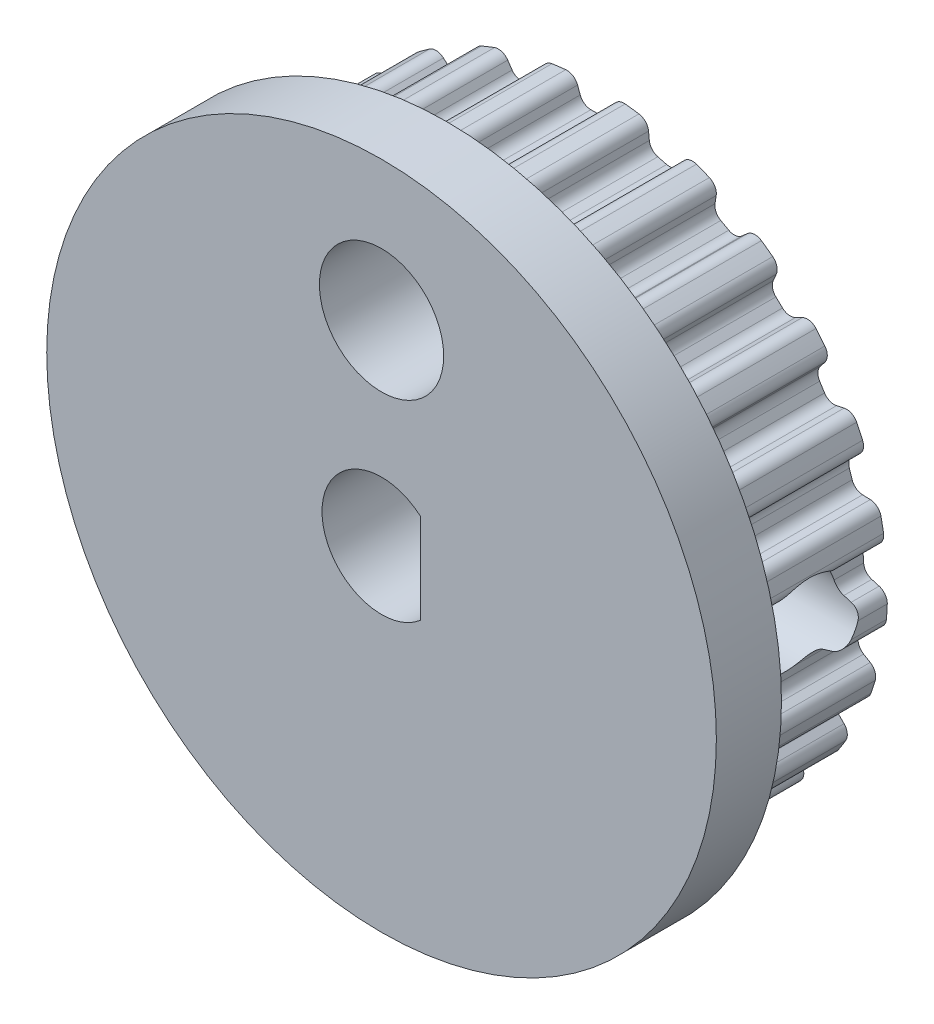
SolidWorks part; units mm, degrees
ref_plane "Front Plane" through (0, 0, 0) normal (0, 0, 1) x (1, 0, 0)
ref_plane "Top Plane" through (0, 0, 0) normal (0, 1, 0) x (1, 0, 0)
ref_plane "Right Plane" through (0, 0, 0) normal (1, 0, 0) x (0, 0, -1)
ref_plane "Plane1" through (0, 0, -5.3) normal (0, 0, -1) x (-1, 0, 0)
sketch "Sketch1" plane through (0, 0, -5.3) normal (0, 0, -1) x (-1, 0, 0)
  line L0 (-2.7705, -6.663) -> (-2.5415, -6.7537)
  line L1 (-2.3491, -7.0456) -> (-2.3549, -7.2528)
  line L2 (-1.4305, -7.4901) -> (-1.3357, -7.3057)
  line L3 (-1.0264, -7.1427) -> (-0.7821, -7.1735)
  line L4 (-0.5231, -7.4084) -> (-0.4772, -7.6106)
  line L5 (0.4772, -7.6106) -> (0.5231, -7.4084)
  line L6 (0.7821, -7.1735) -> (1.0264, -7.1427)
  line L7 (1.3357, -7.3057) -> (1.4305, -7.4901)
  line L8 (2.3549, -7.2528) -> (2.3491, -7.0456)
  line L9 (2.5415, -6.7537) -> (2.7705, -6.663)
  line L10 (3.1106, -6.744) -> (3.2483, -6.8991)
  line L11 (4.0846, -6.4393) -> (4.0274, -6.24)
  line L12 (4.1413, -5.9094) -> (4.3405, -5.7647)
  line L13 (4.6901, -5.7586) -> (4.862, -5.8745)
  line L14 (5.5576, -5.2212) -> (5.4527, -5.0424)
  line L15 (5.4808, -4.6939) -> (5.6377, -4.5041)
  line L16 (5.9748, -4.4113) -> (6.1701, -4.4808)
  line L17 (6.6815, -3.6751) -> (6.5354, -3.528)
  line L18 (6.4759, -3.1834) -> (6.5808, -2.9606)
  line L19 (6.8842, -2.7868) -> (7.0906, -2.8056)
  line L20 (7.3855, -1.898) -> (7.2075, -1.7918)
  line L21 (7.0641, -1.4729) -> (7.1103, -1.231)
  line L22 (7.3609, -0.9872) -> (7.5656, -0.9541)
  line L23 (7.6255, -0.0016) -> (7.4266, 0.0569)
  line L24 (7.2085, 0.3301) -> (7.193, 0.5759)
  line L25 (7.3752, 0.8744) -> (7.5652, 0.9574)
  line L26 (7.3864, 1.8948) -> (7.1792, 1.902)
  line L27 (6.8999, 2.1125) -> (6.8238, 2.3467)
  line L28 (6.9261, 2.681) -> (7.0894, 2.8087)
  line L29 (6.6831, 3.6722) -> (6.4806, 3.6277)
  line L30 (6.1578, 3.762) -> (6.0259, 3.9699)
  line L31 (6.0417, 4.3192) -> (6.1682, 4.4835)
  line L32 (5.5599, 5.2188) -> (5.3748, 5.1254)
  line L33 (5.0288, 5.1752) -> (4.8493, 5.3438)
  line L34 (4.7777, 5.6861) -> (4.8594, 5.8766)
  line L35 (4.0874, 6.4376) -> (3.9314, 6.301)
  line L36 (3.5837, 6.2632) -> (3.368, 6.3819)
  line L37 (3.2136, 6.6956) -> (3.2453, 6.9005)
  line L38 (2.358, 7.2518) -> (2.2409, 7.0807)
  line L39 (1.9136, 6.9577) -> (1.675, 7.0189)
  line L40 (1.4475, 7.2844) -> (1.4273, 7.4908)
  line L41 (0.4805, 7.6104) -> (0.4095, 7.4156)
  line L42 (0.1231, 7.215) -> (-0.1231, 7.215)
  line L43 (-0.4095, 7.4156) -> (-0.4805, 7.6104)
  line L44 (-1.4273, 7.4908) -> (-1.4475, 7.2844)
  line L45 (-1.675, 7.0189) -> (-1.9136, 6.9577)
  line L46 (-2.2409, 7.0807) -> (-2.358, 7.2518)
  line L47 (-3.2453, 6.9005) -> (-3.2136, 6.6956)
  line L48 (-3.368, 6.3819) -> (-3.5837, 6.2632)
  line L49 (-3.9314, 6.301) -> (-4.0874, 6.4376)
  line L50 (-4.8594, 5.8766) -> (-4.7777, 5.6861)
  line L51 (-4.8493, 5.3438) -> (-5.0288, 5.1752)
  line L52 (-5.3748, 5.1254) -> (-5.5599, 5.2188)
  line L53 (-6.1682, 4.4835) -> (-6.0417, 4.3192)
  line L54 (-6.0259, 3.9699) -> (-6.1578, 3.762)
  line L55 (-6.4806, 3.6277) -> (-6.6831, 3.6722)
  line L56 (-7.0894, 2.8087) -> (-6.9261, 2.681)
  line L57 (-6.8238, 2.3467) -> (-6.8999, 2.1125)
  line L58 (-7.1792, 1.902) -> (-7.3864, 1.8948)
  line L59 (-7.5652, 0.9574) -> (-7.3752, 0.8744)
  line L60 (-7.193, 0.5759) -> (-7.2085, 0.3301)
  line L61 (-7.4266, 0.0569) -> (-7.6255, -0.0016)
  line L62 (-7.5656, -0.9541) -> (-7.3609, -0.9872)
  line L63 (-7.1103, -1.231) -> (-7.0641, -1.4729)
  line L64 (-7.2075, -1.7918) -> (-7.3855, -1.898)
  line L65 (-7.0906, -2.8056) -> (-6.8842, -2.7868)
  line L66 (-6.5808, -2.9606) -> (-6.4759, -3.1834)
  line L67 (-6.5354, -3.528) -> (-6.6815, -3.6751)
  line L68 (-6.1701, -4.4808) -> (-5.9748, -4.4113)
  line L69 (-5.6377, -4.5041) -> (-5.4808, -4.6939)
  line L70 (-5.4527, -5.0424) -> (-5.5576, -5.2212)
  line L71 (-4.862, -5.8745) -> (-4.6901, -5.7586)
  line L72 (-4.3405, -5.7647) -> (-4.1413, -5.9094)
  line L73 (-4.0274, -6.24) -> (-4.0846, -6.4393)
  line L74 (-3.2483, -6.8991) -> (-3.1106, -6.744)
  arc A2 (-2.5415, -6.7537) -> (-2.3491, -7.0456) centre (-2.6537, -7.0371) cw
  arc A3 (-2.3549, -7.2528) -> (-2.133, -7.5547) centre (-2.0502, -7.2613) ccw
  arc A4 (-2.133, -7.5547) -> (-1.7703, -7.6478) centre (0, 0) ccw
  arc A5 (-1.7703, -7.6478) -> (-1.4305, -7.4901) centre (-1.7016, -7.3508) ccw
  arc A6 (-1.3357, -7.3057) -> (-1.0264, -7.1427) centre (-1.0646, -7.4451) cw
  arc A7 (-0.7821, -7.1735) -> (-0.5231, -7.4084) centre (-0.8203, -7.4759) cw
  arc A8 (-0.4772, -7.6106) -> (-0.1872, -7.8478) centre (-0.1799, -7.5431) ccw
  arc A9 (-0.1872, -7.8478) -> (0.1872, -7.8478) centre (0, 0) ccw
  arc A10 (0.1872, -7.8478) -> (0.4772, -7.6106) centre (0.1799, -7.5431) ccw
  arc A11 (0.5231, -7.4084) -> (0.7821, -7.1735) centre (0.8203, -7.4759) cw
  arc A12 (1.0264, -7.1427) -> (1.3357, -7.3057) centre (1.0646, -7.4451) cw
  arc A13 (1.4305, -7.4901) -> (1.7703, -7.6478) centre (1.7016, -7.3508) ccw
  arc A14 (1.7703, -7.6478) -> (2.133, -7.5547) centre (0, 0) ccw
  arc A15 (2.133, -7.5547) -> (2.3549, -7.2528) centre (2.0502, -7.2613) ccw
  arc A16 (2.3491, -7.0456) -> (2.5415, -6.7537) centre (2.6537, -7.0371) cw
  arc A17 (2.7705, -6.663) -> (3.1106, -6.744) centre (2.8827, -6.9464) cw
  arc A18 (3.2483, -6.8991) -> (3.6166, -6.9672) centre (3.4762, -6.6967) ccw
  arc A19 (3.6166, -6.9672) -> (3.9447, -6.7869) centre (0, 0) ccw
  arc A20 (3.9447, -6.7869) -> (4.0846, -6.4393) centre (3.7916, -6.5233) ccw
  arc A21 (4.0274, -6.24) -> (4.1413, -5.9094) centre (4.3204, -6.156) cw
  arc A22 (4.3405, -5.7647) -> (4.6901, -5.7586) centre (4.5196, -6.0113) cw
  arc A23 (4.862, -5.8745) -> (5.2357, -5.8489) centre (5.0324, -5.6218) ccw
  arc A24 (5.2357, -5.8489) -> (5.5086, -5.5926) centre (0, 0) ccw
  arc A25 (5.5086, -5.5926) -> (5.5576, -5.2212) centre (5.2947, -5.3755) ccw
  arc A26 (5.4527, -5.0424) -> (5.4808, -4.6939) centre (5.7156, -4.8882) cw
  arc A27 (5.6377, -4.5041) -> (5.9748, -4.4113) centre (5.8726, -4.6984) cw
  arc A28 (6.1701, -4.4808) -> (6.5258, -4.3631) centre (6.2724, -4.1937) ccw
  arc A29 (6.5258, -4.3631) -> (6.7264, -4.047) centre (0, 0) ccw
  arc A30 (6.7264, -4.047) -> (6.6815, -3.6751) centre (6.4652, -3.8898) ccw
  arc A31 (6.5354, -3.528) -> (6.4759, -3.1834) centre (6.7517, -3.3132) cw
  arc A32 (6.5808, -2.9606) -> (6.8842, -2.7868) centre (6.8565, -3.0904) cw
  arc A33 (7.0906, -2.8056) -> (7.4058, -2.6031) centre (7.1183, -2.5021) ccw
  arc A34 (7.4058, -2.6031) -> (7.5215, -2.247) centre (0, 0) ccw
  arc A35 (7.5215, -2.247) -> (7.3855, -1.898) centre (7.2295, -2.1598) ccw
  arc A36 (7.2075, -1.7918) -> (7.0641, -1.4729) centre (7.3635, -1.53) cw
  arc A37 (7.1103, -1.231) -> (7.3609, -0.9872) centre (7.4097, -1.2881) cw
  arc A38 (7.5656, -0.9541) -> (7.8205, -0.6796) centre (7.5169, -0.6532) ccw
  arc A39 (7.8205, -0.6796) -> (7.844, -0.3059) centre (0, 0) ccw
  arc A40 (7.844, -0.3059) -> (7.6255, -0.0016) centre (7.5395, -0.294) ccw
  arc A41 (7.4266, 0.0569) -> (7.2085, 0.3301) centre (7.5127, 0.3493) cw
  arc A42 (7.193, 0.5759) -> (7.3752, 0.8744) centre (7.4972, 0.5951) cw
  arc A43 (7.5652, 0.9574) -> (7.7438, 1.2866) centre (7.4432, 1.2367) ccw
  arc A44 (7.7438, 1.2866) -> (7.6737, 1.6544) centre (0, 0) ccw
  arc A45 (7.6737, 1.6544) -> (7.3864, 1.8948) centre (7.3757, 1.5902) ccw
  arc A46 (7.1792, 1.902) -> (6.8999, 2.1125) centre (7.1898, 2.2066) cw
  arc A47 (6.8238, 2.3467) -> (6.9261, 2.681) centre (7.1137, 2.4408) cw
  arc A48 (7.0894, 2.8087) -> (7.1806, 3.172) centre (6.9018, 3.0489) ccw
  arc A49 (7.1806, 3.172) -> (7.0212, 3.5108) centre (0, 0) ccw
  arc A50 (7.0212, 3.5108) -> (6.6831, 3.6722) centre (6.7485, 3.3745) ccw
  arc A51 (6.4806, 3.6277) -> (6.1578, 3.762) centre (6.4152, 3.9254) cw
  arc A52 (6.0259, 3.9699) -> (6.0417, 4.3192) centre (6.2832, 4.1333) cw
  arc A53 (6.1682, 4.4835) -> (6.1661, 4.8581) centre (5.9267, 4.6695) ccw
  arc A54 (6.1661, 4.8581) -> (5.9275, 5.1466) centre (0, 0) ccw
  arc A55 (5.9275, 5.1466) -> (5.5599, 5.2188) centre (5.6973, 4.9468) ccw
  arc A56 (5.3748, 5.1254) -> (5.0288, 5.1752) centre (5.2374, 5.3974) cw
  arc A57 (4.8493, 5.3438) -> (4.7777, 5.6861) centre (5.0579, 5.566) cw
  arc A58 (4.8594, 5.8766) -> (4.7643, 6.2389) centre (4.5793, 5.9967) ccw
  arc A59 (4.7643, 6.2389) -> (4.4613, 6.459) centre (0, 0) ccw
  arc A60 (4.4613, 6.459) -> (4.0874, 6.4376) centre (4.2881, 6.2082) ccw
  arc A61 (3.9314, 6.301) -> (3.5837, 6.2632) centre (3.7306, 6.5303) cw
  arc A62 (3.368, 6.3819) -> (3.2136, 6.6956) centre (3.5148, 6.649) cw
  arc A63 (3.2453, 6.9005) -> (3.063, 7.2278) centre (2.9441, 6.9471) ccw
  arc A64 (3.063, 7.2278) -> (2.7149, 7.3656) centre (0, 0) ccw
  arc A65 (2.7149, 7.3656) -> (2.358, 7.2518) centre (2.6095, 7.0796) ccw
  arc A66 (2.2409, 7.0807) -> (1.9136, 6.9577) centre (1.9894, 7.2529) cw
  arc A67 (1.675, 7.0189) -> (1.4475, 7.2844) centre (1.7508, 7.3142) cw
  arc A68 (1.4273, 7.4908) -> (1.1693, 7.7624) centre (1.1239, 7.461) ccw
  arc A69 (1.1693, 7.7624) -> (0.7979, 7.8093) centre (0, 0) ccw
  arc A70 (0.7979, 7.8093) -> (0.4805, 7.6104) centre (0.7669, 7.5061) ccw
  arc A71 (0.4095, 7.4156) -> (0.1231, 7.215) centre (0.1231, 7.5198) cw
  arc A72 (-0.1231, 7.215) -> (-0.4095, 7.4156) centre (-0.1231, 7.5198) cw
  arc A73 (-0.4805, 7.6104) -> (-0.7979, 7.8093) centre (-0.7669, 7.5061) ccw
  arc A74 (-0.7979, 7.8093) -> (-1.1693, 7.7624) centre (0, 0) ccw
  arc A75 (-1.1693, 7.7624) -> (-1.4273, 7.4908) centre (-1.1239, 7.461) ccw
  arc A76 (-1.4475, 7.2844) -> (-1.675, 7.0189) centre (-1.7508, 7.3142) cw
  arc A77 (-1.9136, 6.9577) -> (-2.2409, 7.0807) centre (-1.9894, 7.2529) cw
  arc A78 (-2.358, 7.2518) -> (-2.7149, 7.3656) centre (-2.6095, 7.0796) ccw
  arc A79 (-2.7149, 7.3656) -> (-3.063, 7.2278) centre (0, 0) ccw
  arc A80 (-3.063, 7.2278) -> (-3.2453, 6.9005) centre (-2.9441, 6.9471) ccw
  arc A81 (-3.2136, 6.6956) -> (-3.368, 6.3819) centre (-3.5148, 6.649) cw
  arc A82 (-3.5837, 6.2632) -> (-3.9314, 6.301) centre (-3.7306, 6.5303) cw
  arc A83 (-4.0874, 6.4376) -> (-4.4613, 6.459) centre (-4.2881, 6.2082) ccw
  arc A84 (-4.4613, 6.459) -> (-4.7643, 6.2389) centre (0, 0) ccw
  arc A85 (-4.7643, 6.2389) -> (-4.8594, 5.8766) centre (-4.5793, 5.9967) ccw
  arc A86 (-4.7777, 5.6861) -> (-4.8493, 5.3438) centre (-5.0579, 5.566) cw
  arc A87 (-5.0288, 5.1752) -> (-5.3748, 5.1254) centre (-5.2374, 5.3974) cw
  arc A88 (-5.5599, 5.2188) -> (-5.9275, 5.1466) centre (-5.6973, 4.9468) ccw
  arc A89 (-5.9275, 5.1466) -> (-6.1661, 4.8581) centre (0, 0) ccw
  arc A90 (-6.1661, 4.8581) -> (-6.1682, 4.4835) centre (-5.9267, 4.6695) ccw
  arc A91 (-6.0417, 4.3192) -> (-6.0259, 3.9699) centre (-6.2832, 4.1333) cw
  arc A92 (-6.1578, 3.762) -> (-6.4806, 3.6277) centre (-6.4152, 3.9254) cw
  arc A93 (-6.6831, 3.6722) -> (-7.0212, 3.5108) centre (-6.7485, 3.3745) ccw
  arc A94 (-7.0212, 3.5108) -> (-7.1806, 3.172) centre (0, 0) ccw
  arc A95 (-7.1806, 3.172) -> (-7.0894, 2.8087) centre (-6.9018, 3.0489) ccw
  arc A96 (-6.9261, 2.681) -> (-6.8238, 2.3467) centre (-7.1137, 2.4408) cw
  arc A97 (-6.8999, 2.1125) -> (-7.1792, 1.902) centre (-7.1898, 2.2066) cw
  arc A98 (-7.3864, 1.8948) -> (-7.6737, 1.6544) centre (-7.3757, 1.5902) ccw
  arc A99 (-7.6737, 1.6544) -> (-7.7438, 1.2866) centre (0, 0) ccw
  arc A100 (-7.7438, 1.2866) -> (-7.5652, 0.9574) centre (-7.4432, 1.2367) ccw
  arc A101 (-7.3752, 0.8744) -> (-7.193, 0.5759) centre (-7.4972, 0.5951) cw
  arc A102 (-7.2085, 0.3301) -> (-7.4266, 0.0569) centre (-7.5127, 0.3493) cw
  arc A103 (-7.6255, -0.0016) -> (-7.844, -0.3059) centre (-7.5395, -0.294) ccw
  arc A104 (-7.844, -0.3059) -> (-7.8205, -0.6796) centre (0, 0) ccw
  arc A105 (-7.8205, -0.6796) -> (-7.5656, -0.9541) centre (-7.5169, -0.6532) ccw
  arc A106 (-7.3609, -0.9872) -> (-7.1103, -1.231) centre (-7.4097, -1.2881) cw
  arc A107 (-7.0641, -1.4729) -> (-7.2075, -1.7918) centre (-7.3635, -1.53) cw
  arc A108 (-7.3855, -1.898) -> (-7.5215, -2.247) centre (-7.2295, -2.1598) ccw
  arc A109 (-7.5215, -2.247) -> (-7.4058, -2.6031) centre (0, 0) ccw
  arc A110 (-7.4058, -2.6031) -> (-7.0906, -2.8056) centre (-7.1183, -2.5021) ccw
  arc A111 (-6.8842, -2.7868) -> (-6.5808, -2.9606) centre (-6.8565, -3.0904) cw
  arc A112 (-6.4759, -3.1834) -> (-6.5354, -3.528) centre (-6.7517, -3.3132) cw
  arc A113 (-6.6815, -3.6751) -> (-6.7264, -4.047) centre (-6.4652, -3.8898) ccw
  arc A114 (-6.7264, -4.047) -> (-6.5258, -4.3631) centre (0, 0) ccw
  arc A115 (-6.5258, -4.3631) -> (-6.1701, -4.4808) centre (-6.2724, -4.1937) ccw
  arc A116 (-5.9748, -4.4113) -> (-5.6377, -4.5041) centre (-5.8726, -4.6984) cw
  arc A117 (-5.4808, -4.6939) -> (-5.4527, -5.0424) centre (-5.7156, -4.8882) cw
  arc A118 (-5.5576, -5.2212) -> (-5.5086, -5.5926) centre (-5.2947, -5.3755) ccw
  arc A119 (-5.5086, -5.5926) -> (-5.2357, -5.8489) centre (0, 0) ccw
  arc A120 (-5.2357, -5.8489) -> (-4.862, -5.8745) centre (-5.0324, -5.6218) ccw
  arc A121 (-4.6901, -5.7586) -> (-4.3405, -5.7647) centre (-4.5196, -6.0113) cw
  arc A122 (-4.1413, -5.9094) -> (-4.0274, -6.24) centre (-4.3204, -6.156) cw
  arc A123 (-4.0846, -6.4393) -> (-3.9447, -6.7869) centre (-3.7916, -6.5233) ccw
  arc A124 (-3.9447, -6.7869) -> (-3.6166, -6.9672) centre (0, 0) ccw
  arc A125 (-3.6166, -6.9672) -> (-3.2483, -6.8991) centre (-3.4762, -6.6967) ccw
  arc A126 (-3.1106, -6.744) -> (-2.7705, -6.663) centre (-2.8827, -6.9464) cw
extrude "Boss-Extrude1" add sketch "Sketch1" against normal blind 4
sketch "Sketch2" plane through (0, 0, -1.3) normal (0, 0, 1) x (1, 0, 0)
  circle A0 centre (0, 0) radius 9
extrude "Boss-Extrude2" add sketch "Sketch2" along normal blind 1.75
sketch "Sketch3" plane through (0, 0, 0.45) normal (0, 0, 1) x (1, 0, 0)
  line L0 (1.0416, 1.2145) -> (1.0416, -1.2145)
  arc A0 (1.0416, 1.2145) -> (1.0416, -1.2145) centre (0, 0) ccw
sketch "Sketch4" plane through (0, 0, -5.3) normal (0, 0, -1) x (-1, 0, 0)
  line L1 (-2.25, -2.25) -> (2.25, -2.25)
  line L2 (-2.25, -2.25) -> (-2.25, 2.25)
  line L3 (-2.25, 2.25) -> (2.25, 2.25)
  line L4 (2.25, -2.25) -> (2.25, 2.25)
  line L5 (-2.25, -2.25) -> (2.25, 2.25) construction
  line L6 (-2.25, 2.25) -> (2.25, -2.25) construction
  point P0 (0, 0)
  dimension "D1" = 4.5
  dimension "D2" = 4.5
extrude "Boss-Extrude3" add sketch "Sketch4" along normal blind 1.75
extrude "Cut-Extrude2" cut sketch "Sketch3" against normal through all
sketch "Sketch5" plane through (0, 0, 0.45) normal (0, 0, 1) x (1, 0, 0)
  circle A0 centre (0, 5.25) radius 1.67
extrude "Cut-Extrude3" cut sketch "Sketch5" against normal through all
sketch "Sketch7" plane through (1.0416, 0, 0) normal (-1, 0, 0) x (0, 0, 1)
  line L0 (-5.3, 0.453) -> (-1.3, 0.453) construction
  line L1 (-5.3, 0.5759) -> (-5.3, 0.3301) construction
  line L2 (-1.3, 0.5759) -> (-1.3, 0.3301) construction
  line L3 (-7.05, 0) -> (-1.3, 0)
  line L4 (-7.05, 2.25) -> (-7.05, -2.25) construction
  line L5 (-1.3, 9) -> (-1.3, -9) construction
  line L6 (-3.3, 0.453) -> (-3.3, 0) construction
  circle A0 centre (-3.3, 0) radius 1.25
  line M2 (0.45, 1.2145) -> (-7.05, 1.2145)
  line M4 (-7.05, -1.2145) -> (0.45, -1.2145)
  dimension "D1" = 2.5
extrude "Cut-Extrude4" cut sketch "Sketch7" against normal blind 10 and the other way blind 1 contours L3 A0 M2 | A0 L3 M4 | A0 M2 | A0 M4
